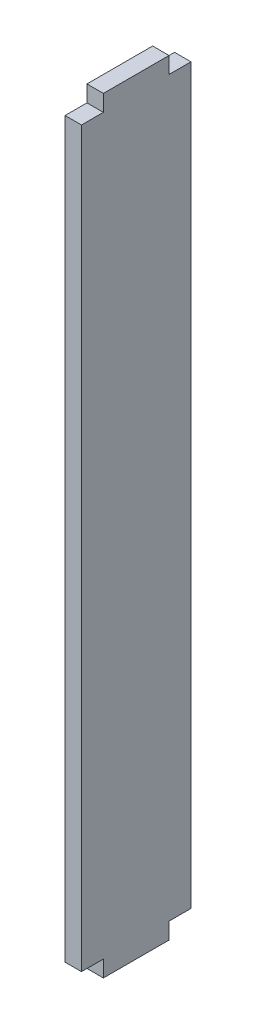
SolidWorks part; units mm, degrees
ref_plane "Front Plane" through (0, 0, 0) normal (0, 0, 1) x (1, 0, 0)
ref_plane "Top Plane" through (0, 0, 0) normal (0, 1, 0) x (1, 0, 0)
ref_plane "Right Plane" through (0, 0, 0) normal (1, 0, 0) x (0, 0, -1)
sketch "Sketch1" plane through (0, 0, 0) normal (1, 0, 0) x (0, 0, -1)
  line L1 (-10, -30.8442) -> (0, -30.8442)
  line L2 (-10, -30.8442) -> (-10, 39.1558)
  line L3 (-10, 39.1558) -> (0, 39.1558)
  line L4 (0, -30.8442) -> (0, 39.1558)
  dimension "D1" = 70
  dimension "D2" = 10
extrude "Boss-Extrude1" add sketch "Sketch1" along normal blind 1.5
sketch "Sketch2" plane through (1.5, 0, 0) normal (1, 0, 0) x (0, 0, -1)
  line L0 (0, 39.1558) -> (-10, 39.1558) construction
  line L1 (-8, 39.1558) -> (-10, 39.1558)
  line L2 (-8, 39.1558) -> (-8, 37.6558)
  line L3 (-8, 37.6558) -> (-10, 37.6558)
  line L4 (-10, 39.1558) -> (-10, 37.6558)
  line L5 (-10, 39.1558) -> (-10, -30.8442) construction
  line L6 (0, -30.8442) -> (0, 39.1558) construction
  line L7 (-2, 39.1558) -> (0, 39.1558)
  line L8 (-2, 39.1558) -> (-2, 37.6558)
  line L9 (-2, 37.6558) -> (0, 37.6558)
  line L10 (0, 39.1558) -> (0, 37.6558)
  line L11 (-10, -30.8442) -> (0, -30.8442) construction
  line L12 (-2, -30.8442) -> (0, -30.8442)
  line L13 (-2, -30.8442) -> (-2, -29.3442)
  line L14 (-2, -29.3442) -> (0, -29.3442)
  line L15 (0, -30.8442) -> (0, -29.3442)
  line L17 (-8, -30.8442) -> (-10, -30.8442)
  line L18 (-8, -30.8442) -> (-8, -29.3442)
  line L19 (-8, -29.3442) -> (-10, -29.3442)
  line L20 (-10, -30.8442) -> (-10, -29.3442)
  dimension "D1" = 1.5
  dimension "D2" = 2
  dimension "D3" = 2
  dimension "D4" = 1.5
extrude "Cut-Extrude1" cut sketch "Sketch2" against normal blind 10
